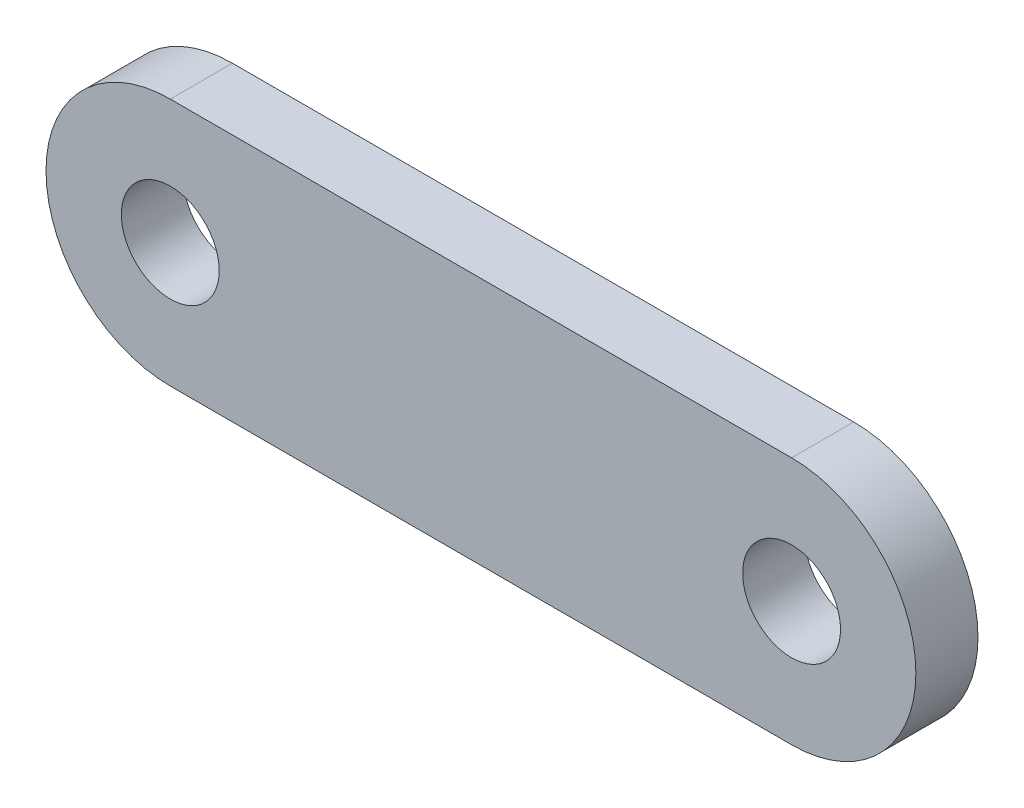
SolidWorks part; units mm, degrees
ref_plane "Front Plane" through (0, 0, 0) normal (0, 0, 1) x (1, 0, 0)
ref_plane "Top Plane" through (0, 0, 0) normal (0, 1, 0) x (1, 0, 0)
ref_plane "Right Plane" through (0, 0, 0) normal (1, 0, 0) x (0, 0, -1)
sketch "Sketch1" plane through (0, 0, 0) normal (0, 0, 1) x (1, 0, 0)
  line L0 (0, 0) -> (20, 0) construction
  line L1 (0, 4) -> (20, 4)
  line L2 (0, -4) -> (20, -4)
  arc A0 (0, 4) -> (0, -4) centre (0, 0) ccw
  arc A1 (20, -4) -> (20, 4) centre (20, 0) ccw
  circle A4 centre (0, 0) radius 1.575
  circle A5 centre (20, 0) radius 1.575
  point P3 (10, 0)
  dimension "D7" = 3.15
  dimension "D8" = 3.15
  dimension "D1" = 20
  dimension "D4" = 8
extrude "Boss-Extrude1" add sketch "Sketch1" along normal blind 2
